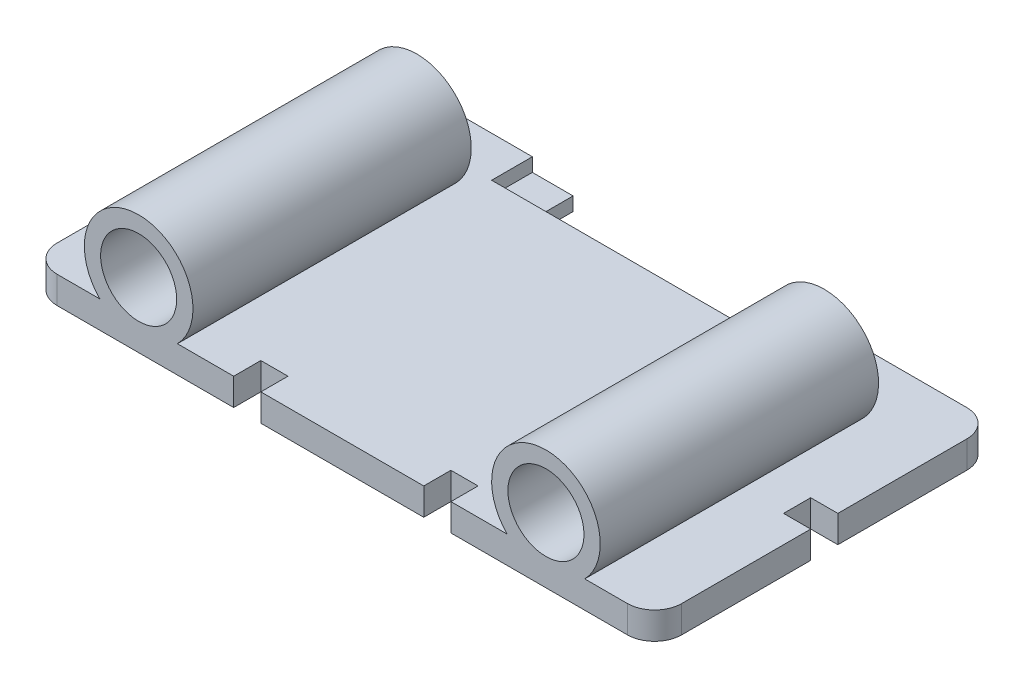
SolidWorks part; units mm, degrees
ref_plane "Front Plane" through (0, 0, 0) normal (0, 0, 1) x (1, 0, 0)
ref_plane "Top Plane" through (0, 0, 0) normal (0, 1, 0) x (1, 0, 0)
ref_plane "Right Plane" through (0, 0, 0) normal (1, 0, 0) x (0, 0, -1)
sketch "Sketch1" plane through (0, 0, 0) normal (0, 1, 0) x (1, 0, 0)
  line L1 (-29.21, -15.875) -> (29.21, -15.875)
  line L2 (-29.21, -15.875) -> (-29.21, 15.875)
  line L3 (-29.21, 15.875) -> (29.21, 15.875)
  line L4 (29.21, -15.875) -> (29.21, 15.875)
  line L5 (-29.21, -15.875) -> (29.21, 15.875) construction
  line L6 (-29.21, 15.875) -> (29.21, -15.875) construction
  point P0 (0, 0)
  dimension "D1" = 58.42
  dimension "D2" = 31.75
extrude "Boss-Extrude1" add sketch "Sketch1" along normal blind 2.54
fillet "Fillet1" radius 2.54 4 edges at (29.21, 1.27, 15.875) (29.21, 1.27, -15.875) (-29.21, 1.27, -15.875) (-29.21, 1.27, 15.875)
sketch "Sketch4" plane through (0, 0, 0) normal (0, 0, 1) x (1, 0, 0)
  line L0 (0, -1.397) -> (0, 1.397) construction
  circle A0 centre (-19.05, 6.096) radius 5.08
  circle A1 centre (19.05, 6.096) radius 5.08
extrude "Boss-Extrude3" add sketch "Sketch4" along normal blind 15.875
sketch "Sketch5" plane through (0, 0, 0) normal (0, 0, -1) x (-1, 0, 0)
  circle A0 centre (-19.05, 6.096) radius 5.08
  circle A1 centre (19.05, 6.096) radius 5.08
extrude "Boss-Extrude4" add sketch "Sketch5" along normal blind 10.16
sketch "Sketch6" plane through (0, 0, 15.875) normal (0, 0, 1) x (1, 0, 0)
  line L0 (0, -1.397) -> (0, 1.397) construction
  circle A0 centre (-19.05, 6.096) radius 3.556
  circle A1 centre (19.05, 6.096) radius 3.556
extrude "Cut-Extrude2" cut sketch "Sketch6" against normal through all
sketch "Sketch9" plane through (0, 2.54, 0) normal (0, 1, 0) x (1, 0, 0)
  line L0 (26.67, 15.875) -> (-26.67, 15.875) construction
  line L1 (-13.97, 15.875) -> (13.97, 15.875)
  line L2 (0, 15.875) -> (0, 12.065)
  line L3 (-13.97, 12.065) -> (13.97, 12.065)
  line L4 (13.97, 15.875) -> (13.97, 12.065)
  line L5 (-13.97, 15.875) -> (-13.97, 12.065)
  line M5 (26.67, 15.875) -> (-26.67, 15.875)
  dimension "D1" = 3.81
  dimension "D2" = 13.97
extrude "Cut-Extrude4" cut sketch "Sketch9" against normal blind 1.27 contours L1 L5 L3 L2 | L4 L2 L3 M5
sketch "Sketch10" plane through (0, 0, 0) normal (0, 1, 0) x (1, 0, 0)
  line L0 (-29.21, 13.335) -> (-29.21, -13.335) construction
  line L12 (-29.21, 0) -> (-26.67, 0)
  line L13 (-29.21, -1.27) -> (-29.21, 1.27)
  line L14 (-29.21, 1.27) -> (-26.67, 1.27)
  line L15 (-26.67, -1.27) -> (-26.67, 1.27)
  line L16 (-29.21, -1.27) -> (-26.67, -1.27)
  line L17 (0, -6.1468) -> (0, 6.1468) construction
  line L18 (29.21, -1.27) -> (26.67, -1.27)
  line L19 (29.21, -1.27) -> (29.21, 1.27)
  line L20 (29.21, 1.27) -> (26.67, 1.27)
  line L21 (26.67, -1.27) -> (26.67, 1.27)
  line L22 (29.21, 0) -> (26.67, 0)
  line L23 (-7.62, 15.875) -> (-10.16, 15.875)
  line L24 (-7.62, 15.875) -> (-7.62, 13.335)
  line L25 (-7.62, 13.335) -> (-10.16, 13.335)
  line L26 (-10.16, 15.875) -> (-10.16, 13.335)
  line L27 (-6.1468, 0) -> (6.1468, 0) construction
  line L28 (-7.62, -13.335) -> (-10.16, -13.335)
  line L29 (-10.16, -15.875) -> (-10.16, -13.335)
  line L30 (-7.62, -15.875) -> (-10.16, -15.875)
  line L31 (-7.62, -15.875) -> (-7.62, -13.335)
  line L32 (7.62, -15.875) -> (7.62, -13.335)
  line L33 (7.62, -15.875) -> (10.16, -15.875)
  line L34 (10.16, -15.875) -> (10.16, -13.335)
  line L35 (7.62, -13.335) -> (10.16, -13.335)
  line L36 (7.62, 13.335) -> (10.16, 13.335)
  line L37 (10.16, 15.875) -> (10.16, 13.335)
  line L38 (7.62, 15.875) -> (10.16, 15.875)
  line L39 (7.62, 15.875) -> (7.62, 13.335)
  line L40 (26.67, 15.875) -> (-26.67, 15.875) construction
  line L41 (-3.81, 19.685) -> (3.81, 19.685)
  line L42 (-3.81, 19.685) -> (-3.81, 12.065)
  line L43 (-3.81, 12.065) -> (3.81, 12.065)
  line L44 (3.81, 19.685) -> (3.81, 12.065)
  line L45 (-3.81, 19.685) -> (3.81, 12.065) construction
  line L46 (-3.81, 12.065) -> (3.81, 19.685) construction
  line L47 (-13.97, 12.065) -> (13.97, 12.065) construction
  line L48 (-10.16, 15.875) -> (10.16, 15.875)
  line L49 (-10.16, 15.875) -> (-10.16, 12.065)
  line L50 (-10.16, 12.065) -> (10.16, 12.065)
  line L51 (10.16, 15.875) -> (10.16, 12.065)
  point P34 (0, 15.875)
  dimension "D1" = 2.54
  dimension "D2" = 2.54
  dimension "D3" = 1.27
  dimension "D4" = 2.54
  dimension "D5" = 7.62
  dimension "D6" = 7.62
extrude "Cut-Extrude6" cut sketch "Sketch10" along normal through all
